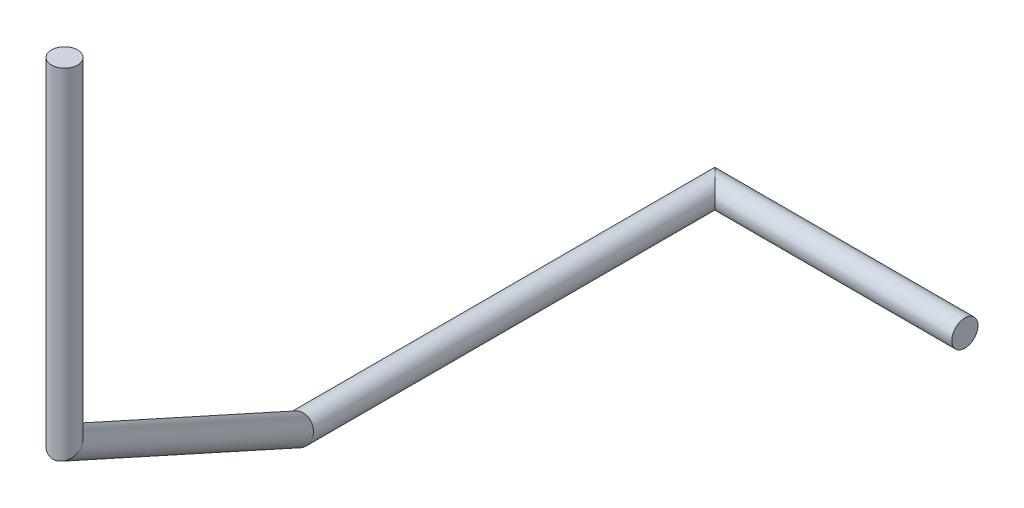
SolidWorks part; units mm, degrees
ref_plane "Front Plane" through (0, 0, 0) normal (0, 0, 1) x (1, 0, 0)
ref_plane "Top Plane" through (0, 0, 0) normal (0, 1, 0) x (1, 0, 0)
ref_plane "Right Plane" through (0, 0, 0) normal (1, 0, 0) x (0, 0, -1)
sketch3d "3DSketch1"
  line L0 (0, 0, 0) -> (-19.05, 0, 0)
  line L1 (-19.05, 0, 0) -> (-19.05, 0, 31.75)
  line L2 (-19.05, 0, 31.75) -> (-10.8255, 16.2481, 57.7581)
  line L3 (-10.8255, 16.2481, 57.7581) -> (-10.8255, 41.6481, 57.7581)
  point P6 (0, 0, 0)
  dimension "D6" = 60
  dimension "D1" = 19.05
  dimension "D2" = 31.75
  dimension "D3" = 31.75
  dimension "D4" = 25.4
  dimension "D5" = 145
sketch "Sketch1" plane through (0, 0, 0) normal (1, 0, 0) x (0, 0, -1)
  circle A0 centre (0, 0) radius 1
  dimension "D1" = 2
sweep "Sweep1" add profiles "Sketch1" path "3DSketch1"
